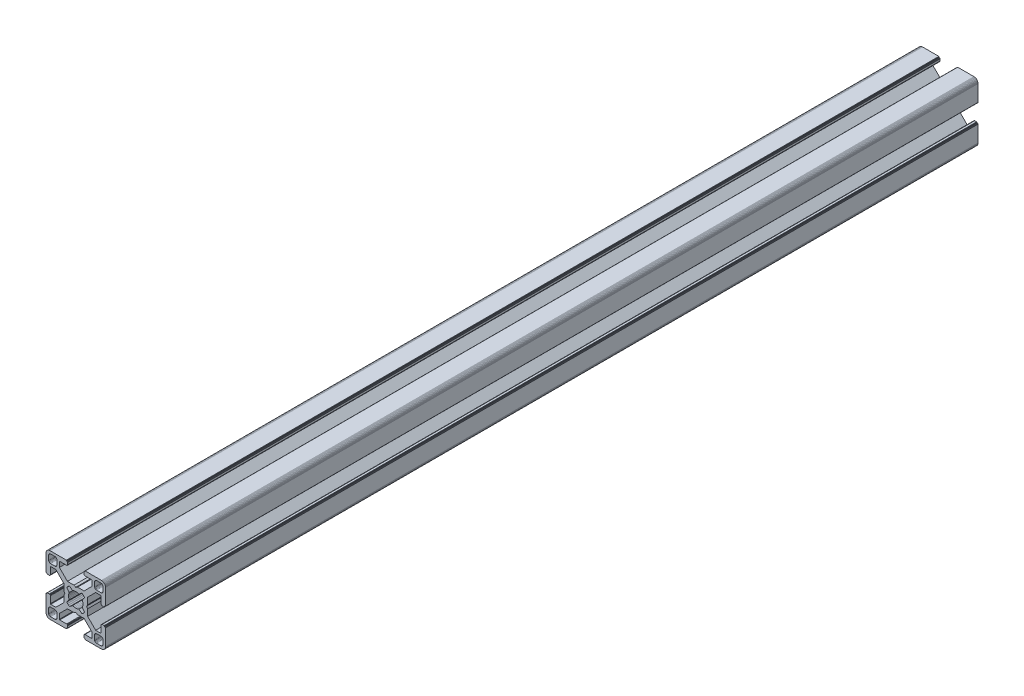
SolidWorks part; units mm, degrees
ref_plane "Front Plane" through (0, 0, 0) normal (0, 0, 1) x (1, 0, 0)
ref_plane "Top Plane" through (0, 0, 0) normal (0, 1, 0) x (1, 0, 0)
ref_plane "Right Plane" through (0, 0, 0) normal (1, 0, 0) x (0, 0, -1)
ref_plane "Plane1" through (0, 0, 0) normal (0, 0, 1) x (1, 0, 0)
sketch "Sketch1" plane through (0, 0, 0) normal (0, 0, 1) x (1, 0, 0)
  line L0 (28.3473, 29.9696) -> (28, 30)
  line L1 (28, 30) -> (19.75, 30)
  line L2 (19.75, 30) -> (19.7153, 29.997)
  line L3 (19.7153, 29.997) -> (19.6816, 29.9879)
  line L4 (19.6816, 29.9879) -> (19.65, 29.9732)
  line L5 (19.65, 29.9732) -> (19.6214, 29.9532)
  line L6 (19.6214, 29.9532) -> (19.5968, 29.9286)
  line L7 (19.5968, 29.9286) -> (19.5768, 29.9)
  line L8 (19.5768, 29.9) -> (19.5621, 29.8684)
  line L9 (19.5621, 29.8684) -> (19.553, 29.8347)
  line L10 (19.553, 29.8347) -> (19.55, 29.8)
  line L11 (19.55, 29.8) -> (19.55, 29.7)
  line L12 (19.55, 29.7) -> (19.547, 29.6653)
  line L13 (19.547, 29.6653) -> (19.5379, 29.6316)
  line L14 (19.5379, 29.6316) -> (19.5232, 29.6)
  line L15 (19.5232, 29.6) -> (19.5032, 29.5714)
  line L16 (19.5032, 29.5714) -> (19.4786, 29.5468)
  line L17 (19.4786, 29.5468) -> (19.45, 29.5268)
  line L18 (19.45, 29.5268) -> (19.4184, 29.5121)
  line L19 (19.4184, 29.5121) -> (19.3847, 29.503)
  line L20 (19.3847, 29.503) -> (19.35, 29.5)
  line L21 (19.35, 29.5) -> (19.25, 29.5)
  line L22 (19.25, 29.5) -> (19.2153, 29.497)
  line L23 (19.2153, 29.497) -> (19.1816, 29.4879)
  line L24 (19.1816, 29.4879) -> (19.15, 29.4732)
  line L25 (19.15, 29.4732) -> (19.1214, 29.4532)
  line L26 (19.1214, 29.4532) -> (19.0968, 29.4286)
  line L27 (19.0968, 29.4286) -> (19.0768, 29.4)
  line L28 (19.0768, 29.4) -> (19.0621, 29.3684)
  line L29 (19.0621, 29.3684) -> (19.053, 29.3347)
  line L30 (19.053, 29.3347) -> (19.05, 29.3)
  line L31 (19.05, 29.3) -> (19.05, 28.4)
  line L32 (19.05, 28.4) -> (19.0591, 28.2958)
  line L33 (19.0591, 28.2958) -> (19.0862, 28.1948)
  line L34 (19.0862, 28.1948) -> (19.1304, 28.1)
  line L35 (19.1304, 28.1) -> (19.1904, 28.0143)
  line L36 (19.1904, 28.0143) -> (19.2643, 27.9404)
  line L37 (19.2643, 27.9404) -> (19.35, 27.8804)
  line L38 (19.35, 27.8804) -> (19.4448, 27.8362)
  line L39 (19.4448, 27.8362) -> (19.5458, 27.8091)
  line L40 (19.5458, 27.8091) -> (19.65, 27.8)
  line L41 (19.65, 27.8) -> (23.05, 27.8)
  line L42 (23.05, 27.8) -> (23.0847, 27.7969)
  line L43 (23.0847, 27.7969) -> (23.1184, 27.7879)
  line L44 (23.1184, 27.7879) -> (23.15, 27.7732)
  line L45 (23.15, 27.7732) -> (23.1786, 27.7532)
  line L46 (23.1786, 27.7532) -> (23.2032, 27.7285)
  line L47 (23.2032, 27.7285) -> (23.2232, 27.7)
  line L48 (23.2232, 27.7) -> (23.2379, 27.6684)
  line L49 (23.2379, 27.6684) -> (23.247, 27.6347)
  line L50 (23.247, 27.6347) -> (23.25, 27.6)
  line L51 (23.25, 27.6) -> (23.25, 25.05)
  line L52 (23.25, 25.05) -> (19.2045, 21)
  line L53 (19.2045, 21) -> (15.9, 21)
  line L54 (15.9, 21) -> (15, 20.4848)
  line L55 (15, 20.4848) -> (14.1, 21)
  line L56 (14.1, 21) -> (10.7955, 21)
  line L57 (10.7955, 21) -> (7.9973, 23.8013)
  line L58 (7.9973, 23.8013) -> (6.75, 25.05)
  line L59 (6.75, 25.05) -> (6.75, 27.6)
  line L60 (6.75, 27.6) -> (6.753, 27.6347)
  line L61 (6.753, 27.6347) -> (6.7621, 27.6684)
  line L62 (6.7621, 27.6684) -> (6.7768, 27.7)
  line L63 (6.7768, 27.7) -> (6.7968, 27.7285)
  line L64 (6.7968, 27.7285) -> (6.8215, 27.7532)
  line L65 (6.8215, 27.7532) -> (6.85, 27.7732)
  line L66 (6.85, 27.7732) -> (6.8816, 27.7879)
  line L67 (6.8816, 27.7879) -> (6.9153, 27.7969)
  line L68 (6.9153, 27.7969) -> (6.95, 27.8)
  line L69 (6.95, 27.8) -> (10.35, 27.8)
  line L70 (10.35, 27.8) -> (10.4542, 27.8091)
  line L71 (10.4542, 27.8091) -> (10.5552, 27.8362)
  line L72 (10.5552, 27.8362) -> (10.65, 27.8804)
  line L73 (10.65, 27.8804) -> (10.7357, 27.9404)
  line L74 (10.7357, 27.9404) -> (10.8096, 28.0143)
  line L75 (10.8096, 28.0143) -> (10.8696, 28.1)
  line L76 (10.8696, 28.1) -> (10.9138, 28.1948)
  line L77 (10.9138, 28.1948) -> (10.9409, 28.2958)
  line L78 (10.9409, 28.2958) -> (10.95, 28.4)
  line L79 (10.95, 28.4) -> (10.95, 29.3)
  line L80 (10.95, 29.3) -> (10.947, 29.3347)
  line L81 (10.947, 29.3347) -> (10.938, 29.3684)
  line L82 (10.938, 29.3684) -> (10.9232, 29.4)
  line L83 (10.9232, 29.4) -> (10.9032, 29.4286)
  line L84 (10.9032, 29.4286) -> (10.8786, 29.4532)
  line L85 (10.8786, 29.4532) -> (10.85, 29.4732)
  line L86 (10.85, 29.4732) -> (10.8184, 29.4879)
  line L87 (10.8184, 29.4879) -> (10.7847, 29.497)
  line L88 (10.7847, 29.497) -> (10.75, 29.5)
  line L89 (10.75, 29.5) -> (10.65, 29.5)
  line L90 (10.65, 29.5) -> (10.6153, 29.503)
  line L91 (10.6153, 29.503) -> (10.5816, 29.5121)
  line L92 (10.5816, 29.5121) -> (10.55, 29.5268)
  line L93 (10.55, 29.5268) -> (10.5214, 29.5468)
  line L94 (10.5214, 29.5468) -> (10.4968, 29.5714)
  line L95 (10.4968, 29.5714) -> (10.4768, 29.6)
  line L96 (10.4768, 29.6) -> (10.4621, 29.6316)
  line L97 (10.4621, 29.6316) -> (10.453, 29.6653)
  line L98 (10.453, 29.6653) -> (10.45, 29.7)
  line L99 (10.45, 29.7) -> (10.45, 29.8)
  line L100 (10.45, 29.8) -> (10.447, 29.8347)
  line L101 (10.447, 29.8347) -> (10.4379, 29.8684)
  line L102 (10.4379, 29.8684) -> (10.4232, 29.9)
  line L103 (10.4232, 29.9) -> (10.4032, 29.9286)
  line L104 (10.4032, 29.9286) -> (10.3786, 29.9532)
  line L105 (10.3786, 29.9532) -> (10.35, 29.9732)
  line L106 (10.35, 29.9732) -> (10.3184, 29.9879)
  line L107 (10.3184, 29.9879) -> (10.2847, 29.997)
  line L108 (10.2847, 29.997) -> (10.25, 30)
  line L109 (10.25, 30) -> (2, 30)
  line L110 (2, 30) -> (1.6527, 29.9696)
  line L111 (1.6527, 29.9696) -> (1.316, 29.8794)
  line L112 (1.316, 29.8794) -> (1, 29.7321)
  line L113 (1, 29.7321) -> (0.7144, 29.5321)
  line L114 (0.7144, 29.5321) -> (0.4679, 29.2856)
  line L115 (0.4679, 29.2856) -> (0.2679, 29)
  line L116 (0.2679, 29) -> (0.1206, 28.684)
  line L117 (0.1206, 28.684) -> (0.0304, 28.3473)
  line L118 (0.0304, 28.3473) -> (0, 28)
  line L119 (0, 28) -> (0, 19.75)
  line L120 (0, 19.75) -> (0.003, 19.7153)
  line L121 (0.003, 19.7153) -> (0.0121, 19.6816)
  line L122 (0.0121, 19.6816) -> (0.0268, 19.65)
  line L123 (0.0268, 19.65) -> (0.0468, 19.6214)
  line L124 (0.0468, 19.6214) -> (0.0714, 19.5968)
  line L125 (0.0714, 19.5968) -> (0.1, 19.5768)
  line L126 (0.1, 19.5768) -> (0.1316, 19.5621)
  line L127 (0.1316, 19.5621) -> (0.1653, 19.553)
  line L128 (0.1653, 19.553) -> (0.2, 19.55)
  line L129 (0.2, 19.55) -> (0.3, 19.55)
  line L130 (0.3, 19.55) -> (0.3347, 19.547)
  line L131 (0.3347, 19.547) -> (0.3684, 19.5379)
  line L132 (0.3684, 19.5379) -> (0.4, 19.5232)
  line L133 (0.4, 19.5232) -> (0.4286, 19.5032)
  line L134 (0.4286, 19.5032) -> (0.4532, 19.4786)
  line L135 (0.4532, 19.4786) -> (0.4732, 19.45)
  line L136 (0.4732, 19.45) -> (0.4879, 19.4184)
  line L137 (0.4879, 19.4184) -> (0.497, 19.3847)
  line L138 (0.497, 19.3847) -> (0.5, 19.35)
  line L139 (0.5, 19.35) -> (0.5, 19.25)
  line L140 (0.5, 19.25) -> (0.503, 19.2153)
  line L141 (0.503, 19.2153) -> (0.5121, 19.1816)
  line L142 (0.5121, 19.1816) -> (0.5268, 19.15)
  line L143 (0.5268, 19.15) -> (0.5468, 19.1214)
  line L144 (0.5468, 19.1214) -> (0.5714, 19.0968)
  line L145 (0.5714, 19.0968) -> (0.6, 19.0768)
  line L146 (0.6, 19.0768) -> (0.6316, 19.0621)
  line L147 (0.6316, 19.0621) -> (0.6653, 19.053)
  line L148 (0.6653, 19.053) -> (0.7, 19.05)
  line L149 (0.7, 19.05) -> (1.6, 19.05)
  line L150 (1.6, 19.05) -> (1.7042, 19.0591)
  line L151 (1.7042, 19.0591) -> (1.8052, 19.0862)
  line L152 (1.8052, 19.0862) -> (1.9, 19.1304)
  line L153 (1.9, 19.1304) -> (1.9857, 19.1904)
  line L154 (1.9857, 19.1904) -> (2.0596, 19.2643)
  line L155 (2.0596, 19.2643) -> (2.1196, 19.35)
  line L156 (2.1196, 19.35) -> (2.1638, 19.4448)
  line L157 (2.1638, 19.4448) -> (2.1909, 19.5458)
  line L158 (2.1909, 19.5458) -> (2.2, 19.65)
  line L159 (2.2, 19.65) -> (2.2, 23.05)
  line L160 (2.2, 23.05) -> (2.203, 23.0847)
  line L161 (2.203, 23.0847) -> (2.2121, 23.1184)
  line L162 (2.2121, 23.1184) -> (2.2268, 23.15)
  line L163 (2.2268, 23.15) -> (2.2468, 23.1786)
  line L164 (2.2468, 23.1786) -> (2.2714, 23.2032)
  line L165 (2.2714, 23.2032) -> (2.3, 23.2232)
  line L166 (2.3, 23.2232) -> (2.3316, 23.2379)
  line L167 (2.3316, 23.2379) -> (2.3653, 23.247)
  line L168 (2.3653, 23.247) -> (2.4, 23.25)
  line L169 (2.4, 23.25) -> (4.95, 23.25)
  line L170 (4.95, 23.25) -> (7.9973, 20.2027)
  line L171 (7.9973, 20.2027) -> (8.9955, 19.2045)
  line L172 (8.9955, 19.2045) -> (8.9955, 15.9)
  line L173 (8.9955, 15.9) -> (9.5151, 15)
  line L174 (9.5151, 15) -> (8.9955, 14.1)
  line L175 (8.9955, 14.1) -> (8.9955, 10.7955)
  line L176 (8.9955, 10.7955) -> (4.95, 6.75)
  line L177 (4.95, 6.75) -> (2.4, 6.75)
  line L178 (2.4, 6.75) -> (2.3653, 6.753)
  line L179 (2.3653, 6.753) -> (2.3316, 6.7621)
  line L180 (2.3316, 6.7621) -> (2.3, 6.7768)
  line L181 (2.3, 6.7768) -> (2.2714, 6.7968)
  line L182 (2.2714, 6.7968) -> (2.2468, 6.8214)
  line L183 (2.2468, 6.8214) -> (2.2268, 6.85)
  line L184 (2.2268, 6.85) -> (2.2121, 6.8816)
  line L185 (2.2121, 6.8816) -> (2.203, 6.9153)
  line L186 (2.203, 6.9153) -> (2.2, 6.95)
  line L187 (2.2, 6.95) -> (2.2, 10.35)
  line L188 (2.2, 10.35) -> (2.1909, 10.4542)
  line L189 (2.1909, 10.4542) -> (2.1638, 10.5552)
  line L190 (2.1638, 10.5552) -> (2.1196, 10.65)
  line L191 (2.1196, 10.65) -> (2.0596, 10.7357)
  line L192 (2.0596, 10.7357) -> (1.9857, 10.8096)
  line L193 (1.9857, 10.8096) -> (1.9, 10.8696)
  line L194 (1.9, 10.8696) -> (1.8052, 10.9138)
  line L195 (1.8052, 10.9138) -> (1.7042, 10.9409)
  line L196 (1.7042, 10.9409) -> (1.6, 10.95)
  line L197 (1.6, 10.95) -> (0.7, 10.95)
  line L198 (0.7, 10.95) -> (0.6653, 10.9469)
  line L199 (0.6653, 10.9469) -> (0.6316, 10.9379)
  line L200 (0.6316, 10.9379) -> (0.6, 10.9232)
  line L201 (0.6, 10.9232) -> (0.5715, 10.9032)
  line L202 (0.5715, 10.9032) -> (0.5468, 10.8785)
  line L203 (0.5468, 10.8785) -> (0.5268, 10.85)
  line L204 (0.5268, 10.85) -> (0.5121, 10.8184)
  line L205 (0.5121, 10.8184) -> (0.503, 10.7847)
  line L206 (0.503, 10.7847) -> (0.5, 10.75)
  line L207 (0.5, 10.75) -> (0.5, 10.65)
  line L208 (0.5, 10.65) -> (0.497, 10.6153)
  line L209 (0.497, 10.6153) -> (0.4879, 10.5816)
  line L210 (0.4879, 10.5816) -> (0.4732, 10.55)
  line L211 (0.4732, 10.55) -> (0.4532, 10.5214)
  line L212 (0.4532, 10.5214) -> (0.4286, 10.4968)
  line L213 (0.4286, 10.4968) -> (0.4, 10.4768)
  line L214 (0.4, 10.4768) -> (0.3684, 10.4621)
  line L215 (0.3684, 10.4621) -> (0.3347, 10.453)
  line L216 (0.3347, 10.453) -> (0.3, 10.45)
  line L217 (0.3, 10.45) -> (0.2, 10.45)
  line L218 (0.2, 10.45) -> (0.1653, 10.447)
  line L219 (0.1653, 10.447) -> (0.1316, 10.4379)
  line L220 (0.1316, 10.4379) -> (0.1, 10.4232)
  line L221 (0.1, 10.4232) -> (0.0714, 10.4032)
  line L222 (0.0714, 10.4032) -> (0.0468, 10.3786)
  line L223 (0.0468, 10.3786) -> (0.0268, 10.35)
  line L224 (0.0268, 10.35) -> (0.0121, 10.3184)
  line L225 (0.0121, 10.3184) -> (0.003, 10.2847)
  line L226 (0.003, 10.2847) -> (0, 10.25)
  line L227 (0, 10.25) -> (0, 2)
  line L228 (0, 2) -> (0.0304, 1.6527)
  line L229 (0.0304, 1.6527) -> (0.1206, 1.316)
  line L230 (0.1206, 1.316) -> (0.2679, 1)
  line L231 (0.2679, 1) -> (0.4679, 0.7144)
  line L232 (0.4679, 0.7144) -> (0.7144, 0.4679)
  line L233 (0.7144, 0.4679) -> (1, 0.2679)
  line L234 (1, 0.2679) -> (1.316, 0.1206)
  line L235 (1.316, 0.1206) -> (1.6527, 0.0304)
  line L236 (1.6527, 0.0304) -> (2, 0)
  line L237 (2, 0) -> (10.25, 0)
  line L238 (10.25, 0) -> (10.2847, 0.003)
  line L239 (10.2847, 0.003) -> (10.3184, 0.0121)
  line L240 (10.3184, 0.0121) -> (10.35, 0.0268)
  line L241 (10.35, 0.0268) -> (10.3786, 0.0468)
  line L242 (10.3786, 0.0468) -> (10.4032, 0.0714)
  line L243 (10.4032, 0.0714) -> (10.4232, 0.1)
  line L244 (10.4232, 0.1) -> (10.4379, 0.1316)
  line L245 (10.4379, 0.1316) -> (10.447, 0.1653)
  line L246 (10.447, 0.1653) -> (10.45, 0.2)
  line L247 (10.45, 0.2) -> (10.45, 0.3)
  line L248 (10.45, 0.3) -> (10.453, 0.3347)
  line L249 (10.453, 0.3347) -> (10.4621, 0.3684)
  line L250 (10.4621, 0.3684) -> (10.4768, 0.4)
  line L251 (10.4768, 0.4) -> (10.4968, 0.4286)
  line L252 (10.4968, 0.4286) -> (10.5214, 0.4532)
  line L253 (10.5214, 0.4532) -> (10.55, 0.4732)
  line L254 (10.55, 0.4732) -> (10.5816, 0.4879)
  line L255 (10.5816, 0.4879) -> (10.6153, 0.497)
  line L256 (10.6153, 0.497) -> (10.65, 0.5)
  line L257 (10.65, 0.5) -> (10.75, 0.5)
  line L258 (10.75, 0.5) -> (10.7847, 0.503)
  line L259 (10.7847, 0.503) -> (10.8184, 0.5121)
  line L260 (10.8184, 0.5121) -> (10.85, 0.5268)
  line L261 (10.85, 0.5268) -> (10.8785, 0.5468)
  line L262 (10.8785, 0.5468) -> (10.9032, 0.5715)
  line L263 (10.9032, 0.5715) -> (10.9232, 0.6)
  line L264 (10.9232, 0.6) -> (10.9379, 0.6316)
  line L265 (10.9379, 0.6316) -> (10.9469, 0.6653)
  line L266 (10.9469, 0.6653) -> (10.95, 0.7)
  line L267 (10.95, 0.7) -> (10.95, 1.6)
  line L268 (10.95, 1.6) -> (10.9409, 1.7042)
  line L269 (10.9409, 1.7042) -> (10.9138, 1.8052)
  line L270 (10.9138, 1.8052) -> (10.8696, 1.9)
  line L271 (10.8696, 1.9) -> (10.8096, 1.9857)
  line L272 (10.8096, 1.9857) -> (10.7357, 2.0596)
  line L273 (10.7357, 2.0596) -> (10.65, 2.1196)
  line L274 (10.65, 2.1196) -> (10.5552, 2.1638)
  line L275 (10.5552, 2.1638) -> (10.4542, 2.1909)
  line L276 (10.4542, 2.1909) -> (10.35, 2.2)
  line L277 (10.35, 2.2) -> (6.95, 2.2)
  line L278 (6.95, 2.2) -> (6.9153, 2.203)
  line L279 (6.9153, 2.203) -> (6.8816, 2.212)
  line L280 (6.8816, 2.212) -> (6.85, 2.2268)
  line L281 (6.85, 2.2268) -> (6.8215, 2.2468)
  line L282 (6.8215, 2.2468) -> (6.7968, 2.2714)
  line L283 (6.7968, 2.2714) -> (6.7768, 2.3)
  line L284 (6.7768, 2.3) -> (6.7621, 2.3316)
  line L285 (6.7621, 2.3316) -> (6.753, 2.3653)
  line L286 (6.753, 2.3653) -> (6.75, 2.4)
  line L287 (6.75, 2.4) -> (6.75, 4.95)
  line L288 (6.75, 4.95) -> (9.7875, 7.9908)
  line L289 (9.7875, 7.9908) -> (10.7955, 9)
  line L290 (10.7955, 9) -> (14.1, 9)
  line L291 (14.1, 9) -> (15, 9.5151)
  line L292 (15, 9.5151) -> (15.9, 9)
  line L293 (15.9, 9) -> (19.2045, 9)
  line L294 (19.2045, 9) -> (20.2126, 7.9908)
  line L295 (20.2126, 7.9908) -> (23.25, 4.95)
  line L296 (23.25, 4.95) -> (23.25, 2.4)
  line L297 (23.25, 2.4) -> (23.247, 2.3653)
  line L298 (23.247, 2.3653) -> (23.2379, 2.3316)
  line L299 (23.2379, 2.3316) -> (23.2232, 2.3)
  line L300 (23.2232, 2.3) -> (23.2032, 2.2714)
  line L301 (23.2032, 2.2714) -> (23.1786, 2.2468)
  line L302 (23.1786, 2.2468) -> (23.15, 2.2268)
  line L303 (23.15, 2.2268) -> (23.1184, 2.212)
  line L304 (23.1184, 2.212) -> (23.0847, 2.203)
  line L305 (23.0847, 2.203) -> (23.05, 2.2)
  line L306 (23.05, 2.2) -> (19.65, 2.2)
  line L307 (19.65, 2.2) -> (19.5458, 2.1909)
  line L308 (19.5458, 2.1909) -> (19.4448, 2.1638)
  line L309 (19.4448, 2.1638) -> (19.35, 2.1196)
  line L310 (19.35, 2.1196) -> (19.2643, 2.0596)
  line L311 (19.2643, 2.0596) -> (19.1904, 1.9857)
  line L312 (19.1904, 1.9857) -> (19.1304, 1.9)
  line L313 (19.1304, 1.9) -> (19.0862, 1.8052)
  line L314 (19.0862, 1.8052) -> (19.0591, 1.7042)
  line L315 (19.0591, 1.7042) -> (19.05, 1.6)
  line L316 (19.05, 1.6) -> (19.05, 0.7)
  line L317 (19.05, 0.7) -> (19.053, 0.6653)
  line L318 (19.053, 0.6653) -> (19.0621, 0.6316)
  line L319 (19.0621, 0.6316) -> (19.0768, 0.6)
  line L320 (19.0768, 0.6) -> (19.0968, 0.5714)
  line L321 (19.0968, 0.5714) -> (19.1214, 0.5468)
  line L322 (19.1214, 0.5468) -> (19.15, 0.5268)
  line L323 (19.15, 0.5268) -> (19.1816, 0.5121)
  line L324 (19.1816, 0.5121) -> (19.2153, 0.503)
  line L325 (19.2153, 0.503) -> (19.25, 0.5)
  line L326 (19.25, 0.5) -> (19.35, 0.5)
  line L327 (19.35, 0.5) -> (19.3847, 0.497)
  line L328 (19.3847, 0.497) -> (19.4184, 0.4879)
  line L329 (19.4184, 0.4879) -> (19.45, 0.4732)
  line L330 (19.45, 0.4732) -> (19.4786, 0.4532)
  line L331 (19.4786, 0.4532) -> (19.5032, 0.4286)
  line L332 (19.5032, 0.4286) -> (19.5232, 0.4)
  line L333 (19.5232, 0.4) -> (19.5379, 0.3684)
  line L334 (19.5379, 0.3684) -> (19.547, 0.3347)
  line L335 (19.547, 0.3347) -> (19.55, 0.3)
  line L336 (19.55, 0.3) -> (19.55, 0.2)
  line L337 (19.55, 0.2) -> (19.553, 0.1653)
  line L338 (19.553, 0.1653) -> (19.5621, 0.1316)
  line L339 (19.5621, 0.1316) -> (19.5768, 0.1)
  line L340 (19.5768, 0.1) -> (19.5968, 0.0714)
  line L341 (19.5968, 0.0714) -> (19.6214, 0.0468)
  line L342 (19.6214, 0.0468) -> (19.65, 0.0268)
  line L343 (19.65, 0.0268) -> (19.6816, 0.0121)
  line L344 (19.6816, 0.0121) -> (19.7153, 0.003)
  line L345 (19.7153, 0.003) -> (19.75, 0)
  line L346 (19.75, 0) -> (28, 0)
  line L347 (28, 0) -> (28.3473, 0.0304)
  line L348 (28.3473, 0.0304) -> (28.684, 0.1206)
  line L349 (28.684, 0.1206) -> (29, 0.2679)
  line L350 (29, 0.2679) -> (29.2856, 0.4679)
  line L351 (29.2856, 0.4679) -> (29.5321, 0.7144)
  line L352 (29.5321, 0.7144) -> (29.7321, 1)
  line L353 (29.7321, 1) -> (29.8794, 1.316)
  line L354 (29.8794, 1.316) -> (29.9696, 1.6527)
  line L355 (29.9696, 1.6527) -> (30, 2)
  line L356 (30, 2) -> (30, 10.25)
  line L357 (30, 10.25) -> (29.997, 10.2847)
  line L358 (29.997, 10.2847) -> (29.988, 10.3184)
  line L359 (29.988, 10.3184) -> (29.9732, 10.35)
  line L360 (29.9732, 10.35) -> (29.9532, 10.3785)
  line L361 (29.9532, 10.3785) -> (29.9286, 10.4032)
  line L362 (29.9286, 10.4032) -> (29.9, 10.4232)
  line L363 (29.9, 10.4232) -> (29.8684, 10.4379)
  line L364 (29.8684, 10.4379) -> (29.8347, 10.447)
  line L365 (29.8347, 10.447) -> (29.8, 10.45)
  line L366 (29.8, 10.45) -> (29.7, 10.45)
  line L367 (29.7, 10.45) -> (29.6649, 10.4534)
  line L368 (29.6649, 10.4534) -> (29.6312, 10.4624)
  line L369 (29.6312, 10.4624) -> (29.5996, 10.4772)
  line L370 (29.5996, 10.4772) -> (29.5711, 10.4972)
  line L371 (29.5711, 10.4972) -> (29.5464, 10.5218)
  line L372 (29.5464, 10.5218) -> (29.5264, 10.5504)
  line L373 (29.5264, 10.5504) -> (29.5117, 10.582)
  line L374 (29.5117, 10.582) -> (29.5027, 10.6156)
  line L375 (29.5027, 10.6156) -> (29.4996, 10.6504)
  line L376 (29.4996, 10.6504) -> (29.4996, 10.7504)
  line L377 (29.4996, 10.7504) -> (29.497, 10.7847)
  line L378 (29.497, 10.7847) -> (29.4879, 10.8184)
  line L379 (29.4879, 10.8184) -> (29.4732, 10.85)
  line L380 (29.4732, 10.85) -> (29.4532, 10.8785)
  line L381 (29.4532, 10.8785) -> (29.4286, 10.9032)
  line L382 (29.4286, 10.9032) -> (29.4, 10.9232)
  line L383 (29.4, 10.9232) -> (29.3684, 10.9379)
  line L384 (29.3684, 10.9379) -> (29.3347, 10.9469)
  line L385 (29.3347, 10.9469) -> (29.3, 10.95)
  line L386 (29.3, 10.95) -> (28.4, 10.95)
  line L387 (28.4, 10.95) -> (28.2958, 10.9409)
  line L388 (28.2958, 10.9409) -> (28.1948, 10.9138)
  line L389 (28.1948, 10.9138) -> (28.1, 10.8696)
  line L390 (28.1, 10.8696) -> (28.0143, 10.8096)
  line L391 (28.0143, 10.8096) -> (27.9404, 10.7357)
  line L392 (27.9404, 10.7357) -> (27.8804, 10.65)
  line L393 (27.8804, 10.65) -> (27.8362, 10.5552)
  line L394 (27.8362, 10.5552) -> (27.8091, 10.4542)
  line L395 (27.8091, 10.4542) -> (27.8, 10.35)
  line L396 (27.8, 10.35) -> (27.8, 6.95)
  line L397 (27.8, 6.95) -> (27.797, 6.9153)
  line L398 (27.797, 6.9153) -> (27.7879, 6.8816)
  line L399 (27.7879, 6.8816) -> (27.7732, 6.85)
  line L400 (27.7732, 6.85) -> (27.7532, 6.8214)
  line L401 (27.7532, 6.8214) -> (27.7286, 6.7968)
  line L402 (27.7286, 6.7968) -> (27.7, 6.7768)
  line L403 (27.7, 6.7768) -> (27.6684, 6.7621)
  line L404 (27.6684, 6.7621) -> (27.6347, 6.753)
  line L405 (27.6347, 6.753) -> (27.6, 6.75)
  line L406 (27.6, 6.75) -> (25.05, 6.75)
  line L407 (25.05, 6.75) -> (23.8092, 7.9908)
  line L408 (23.8092, 7.9908) -> (21.0045, 10.7955)
  line L409 (21.0045, 10.7955) -> (21.0045, 14.1)
  line L410 (21.0045, 14.1) -> (20.4849, 15)
  line L411 (20.4849, 15) -> (21.0045, 15.9)
  line L412 (21.0045, 15.9) -> (21.0045, 19.2045)
  line L413 (21.0045, 19.2045) -> (25.05, 23.25)
  line L414 (25.05, 23.25) -> (27.6, 23.25)
  line L415 (27.6, 23.25) -> (27.6347, 23.247)
  line L416 (27.6347, 23.247) -> (27.6684, 23.2379)
  line L417 (27.6684, 23.2379) -> (27.7, 23.2232)
  line L418 (27.7, 23.2232) -> (27.7286, 23.2032)
  line L419 (27.7286, 23.2032) -> (27.7532, 23.1786)
  line L420 (27.7532, 23.1786) -> (27.7732, 23.15)
  line L421 (27.7732, 23.15) -> (27.7879, 23.1184)
  line L422 (27.7879, 23.1184) -> (27.797, 23.0847)
  line L423 (27.797, 23.0847) -> (27.8, 23.05)
  line L424 (27.8, 23.05) -> (27.8, 19.65)
  line L425 (27.8, 19.65) -> (27.8091, 19.5458)
  line L426 (27.8091, 19.5458) -> (27.8362, 19.4448)
  line L427 (27.8362, 19.4448) -> (27.8804, 19.35)
  line L428 (27.8804, 19.35) -> (27.9404, 19.2643)
  line L429 (27.9404, 19.2643) -> (28.0143, 19.1904)
  line L430 (28.0143, 19.1904) -> (28.1, 19.1304)
  line L431 (28.1, 19.1304) -> (28.1948, 19.0862)
  line L432 (28.1948, 19.0862) -> (28.2958, 19.0591)
  line L433 (28.2958, 19.0591) -> (28.4, 19.05)
  line L434 (28.4, 19.05) -> (29.3, 19.05)
  line L435 (29.3, 19.05) -> (29.3347, 19.053)
  line L436 (29.3347, 19.053) -> (29.3684, 19.0621)
  line L437 (29.3684, 19.0621) -> (29.4, 19.0768)
  line L438 (29.4, 19.0768) -> (29.4282, 19.0971)
  line L439 (29.4282, 19.0971) -> (29.4528, 19.1218)
  line L440 (29.4528, 19.1218) -> (29.4728, 19.1504)
  line L441 (29.4728, 19.1504) -> (29.4876, 19.182)
  line L442 (29.4876, 19.182) -> (29.4966, 19.2156)
  line L443 (29.4966, 19.2156) -> (29.4996, 19.2504)
  line L444 (29.4996, 19.2504) -> (29.4996, 19.3504)
  line L445 (29.4996, 19.3504) -> (29.5027, 19.3851)
  line L446 (29.5027, 19.3851) -> (29.5117, 19.4188)
  line L447 (29.5117, 19.4188) -> (29.5264, 19.4504)
  line L448 (29.5264, 19.4504) -> (29.5464, 19.4789)
  line L449 (29.5464, 19.4789) -> (29.5711, 19.5036)
  line L450 (29.5711, 19.5036) -> (29.5996, 19.5236)
  line L451 (29.5996, 19.5236) -> (29.6312, 19.5383)
  line L452 (29.6312, 19.5383) -> (29.6649, 19.5473)
  line L453 (29.6649, 19.5473) -> (29.7, 19.55)
  line L454 (29.7, 19.55) -> (29.8, 19.55)
  line L455 (29.8, 19.55) -> (29.8347, 19.553)
  line L456 (29.8347, 19.553) -> (29.8684, 19.5621)
  line L457 (29.8684, 19.5621) -> (29.9, 19.5768)
  line L458 (29.9, 19.5768) -> (29.9286, 19.5968)
  line L459 (29.9286, 19.5968) -> (29.9532, 19.6214)
  line L460 (29.9532, 19.6214) -> (29.9732, 19.65)
  line L461 (29.9732, 19.65) -> (29.9879, 19.6816)
  line L462 (29.9879, 19.6816) -> (29.997, 19.7153)
  line L463 (29.997, 19.7153) -> (30, 19.75)
  line L464 (30, 19.75) -> (30, 28)
  line L465 (30, 28) -> (29.9696, 28.3473)
  line L466 (29.9696, 28.3473) -> (29.8794, 28.684)
  line L467 (29.8794, 28.684) -> (29.7321, 29)
  line L468 (29.7321, 29) -> (29.5321, 29.2856)
  line L469 (29.5321, 29.2856) -> (29.2856, 29.5321)
  line L470 (29.2856, 29.5321) -> (29, 29.7321)
  line L471 (29, 29.7321) -> (28.684, 29.8794)
  line L472 (28.684, 29.8794) -> (28.3473, 29.9696)
  line L473 (1.3, 25.5) -> (1.3, 27.7)
  line L474 (1.3, 27.7) -> (1.3123, 27.8564)
  line L475 (1.3123, 27.8564) -> (1.3489, 28.009)
  line L476 (1.3489, 28.009) -> (1.409, 28.154)
  line L477 (1.409, 28.154) -> (1.491, 28.2878)
  line L478 (1.491, 28.2878) -> (1.5929, 28.4071)
  line L479 (1.5929, 28.4071) -> (1.7122, 28.509)
  line L480 (1.7122, 28.509) -> (1.846, 28.591)
  line L481 (1.846, 28.591) -> (1.991, 28.6511)
  line L482 (1.991, 28.6511) -> (2.1436, 28.6877)
  line L483 (2.1436, 28.6877) -> (2.3, 28.7)
  line L484 (2.3, 28.7) -> (4.5, 28.7)
  line L485 (4.5, 28.7) -> (4.6564, 28.6877)
  line L486 (4.6564, 28.6877) -> (4.809, 28.6511)
  line L487 (4.809, 28.6511) -> (4.954, 28.591)
  line L488 (4.954, 28.591) -> (5.0878, 28.509)
  line L489 (5.0878, 28.509) -> (5.2071, 28.4071)
  line L490 (5.2071, 28.4071) -> (5.309, 28.2878)
  line L491 (5.309, 28.2878) -> (5.391, 28.154)
  line L492 (5.391, 28.154) -> (5.4511, 28.009)
  line L493 (5.4511, 28.009) -> (5.4877, 27.8564)
  line L494 (5.4877, 27.8564) -> (5.5, 27.7)
  line L495 (5.5, 27.7) -> (5.5, 25.5)
  line L496 (5.5, 25.5) -> (5.4877, 25.3436)
  line L497 (5.4877, 25.3436) -> (5.4511, 25.191)
  line L498 (5.4511, 25.191) -> (5.391, 25.046)
  line L499 (5.391, 25.046) -> (5.309, 24.9122)
  line L500 (5.309, 24.9122) -> (5.2071, 24.7929)
  line L501 (5.2071, 24.7929) -> (5.0878, 24.691)
  line L502 (5.0878, 24.691) -> (4.954, 24.609)
  line L503 (4.954, 24.609) -> (4.809, 24.5489)
  line L504 (4.809, 24.5489) -> (4.6564, 24.5123)
  line L505 (4.6564, 24.5123) -> (4.5, 24.5)
  line L506 (4.5, 24.5) -> (2.3, 24.5)
  line L507 (2.3, 24.5) -> (2.1436, 24.5123)
  line L508 (2.1436, 24.5123) -> (1.991, 24.5489)
  line L509 (1.991, 24.5489) -> (1.846, 24.609)
  line L510 (1.846, 24.609) -> (1.7122, 24.691)
  line L511 (1.7122, 24.691) -> (1.5929, 24.7929)
  line L512 (1.5929, 24.7929) -> (1.491, 24.9122)
  line L513 (1.491, 24.9122) -> (1.409, 25.046)
  line L514 (1.409, 25.046) -> (1.3489, 25.191)
  line L515 (1.3489, 25.191) -> (1.3123, 25.3436)
  line L516 (1.3123, 25.3436) -> (1.3, 25.5)
  line L517 (25.3436, 28.6877) -> (25.5, 28.7)
  line L518 (25.5, 28.7) -> (27.7, 28.7)
  line L519 (27.7, 28.7) -> (27.8564, 28.6877)
  line L520 (27.8564, 28.6877) -> (28.009, 28.6511)
  line L521 (28.009, 28.6511) -> (28.154, 28.591)
  line L522 (28.154, 28.591) -> (28.2878, 28.509)
  line L523 (28.2878, 28.509) -> (28.4071, 28.4071)
  line L524 (28.4071, 28.4071) -> (28.509, 28.2878)
  line L525 (28.509, 28.2878) -> (28.591, 28.154)
  line L526 (28.591, 28.154) -> (28.6511, 28.009)
  line L527 (28.6511, 28.009) -> (28.6877, 27.8564)
  line L528 (28.6877, 27.8564) -> (28.7, 27.7)
  line L529 (28.7, 27.7) -> (28.7, 25.5)
  line L530 (28.7, 25.5) -> (28.6877, 25.3436)
  line L531 (28.6877, 25.3436) -> (28.6511, 25.191)
  line L532 (28.6511, 25.191) -> (28.591, 25.046)
  line L533 (28.591, 25.046) -> (28.509, 24.9122)
  line L534 (28.509, 24.9122) -> (28.4071, 24.7929)
  line L535 (28.4071, 24.7929) -> (28.2878, 24.691)
  line L536 (28.2878, 24.691) -> (28.154, 24.609)
  line L537 (28.154, 24.609) -> (28.009, 24.5489)
  line L538 (28.009, 24.5489) -> (27.8564, 24.5123)
  line L539 (27.8564, 24.5123) -> (27.7, 24.5)
  line L540 (27.7, 24.5) -> (25.5, 24.5)
  line L541 (25.5, 24.5) -> (25.3436, 24.5123)
  line L542 (25.3436, 24.5123) -> (25.191, 24.5489)
  line L543 (25.191, 24.5489) -> (25.046, 24.609)
  line L544 (25.046, 24.609) -> (24.9122, 24.691)
  line L545 (24.9122, 24.691) -> (24.7929, 24.7929)
  line L546 (24.7929, 24.7929) -> (24.691, 24.9122)
  line L547 (24.691, 24.9122) -> (24.609, 25.046)
  line L548 (24.609, 25.046) -> (24.5489, 25.191)
  line L549 (24.5489, 25.191) -> (24.5123, 25.3436)
  line L550 (24.5123, 25.3436) -> (24.5, 25.5)
  line L551 (24.5, 25.5) -> (24.5, 27.7)
  line L552 (24.5, 27.7) -> (24.5123, 27.8564)
  line L553 (24.5123, 27.8564) -> (24.5489, 28.009)
  line L554 (24.5489, 28.009) -> (24.609, 28.154)
  line L555 (24.609, 28.154) -> (24.691, 28.2878)
  line L556 (24.691, 28.2878) -> (24.7929, 28.4071)
  line L557 (24.7929, 28.4071) -> (24.9122, 28.509)
  line L558 (24.9122, 28.509) -> (25.046, 28.591)
  line L559 (25.046, 28.591) -> (25.191, 28.6511)
  line L560 (25.191, 28.6511) -> (25.3436, 28.6877)
  line L561 (15, 18.65) -> (15.55, 18.6083)
  line L562 (15.55, 18.6083) -> (16.0875, 18.4842)
  line L563 (16.0875, 18.4842) -> (16.6001, 18.2806)
  line L564 (16.6001, 18.2806) -> (18.1359, 19.5184)
  line L565 (18.1359, 19.5184) -> (18.645, 19.1187)
  line L566 (18.645, 19.1187) -> (19.1036, 18.6621)
  line L567 (19.1036, 18.6621) -> (19.5053, 18.1547)
  line L568 (19.5053, 18.1547) -> (18.2806, 16.6001)
  line L569 (18.2806, 16.6001) -> (18.4842, 16.0875)
  line L570 (18.4842, 16.0875) -> (18.6083, 15.55)
  line L571 (18.6083, 15.55) -> (18.65, 15)
  line L572 (18.65, 15) -> (18.6083, 14.45)
  line L573 (18.6083, 14.45) -> (18.4842, 13.9125)
  line L574 (18.4842, 13.9125) -> (18.2806, 13.3999)
  line L575 (18.2806, 13.3999) -> (19.5053, 11.8453)
  line L576 (19.5053, 11.8453) -> (19.1036, 11.3379)
  line L577 (19.1036, 11.3379) -> (18.645, 10.8813)
  line L578 (18.645, 10.8813) -> (18.1359, 10.4816)
  line L579 (18.1359, 10.4816) -> (16.6001, 11.7194)
  line L580 (16.6001, 11.7194) -> (16.0875, 11.5158)
  line L581 (16.0875, 11.5158) -> (15.55, 11.3917)
  line L582 (15.55, 11.3917) -> (15, 11.35)
  line L583 (15, 11.35) -> (14.45, 11.3917)
  line L584 (14.45, 11.3917) -> (13.9125, 11.5158)
  line L585 (13.9125, 11.5158) -> (13.3999, 11.7194)
  line L586 (13.3999, 11.7194) -> (11.8641, 10.4816)
  line L587 (11.8641, 10.4816) -> (11.355, 10.8813)
  line L588 (11.355, 10.8813) -> (10.8964, 11.3379)
  line L589 (10.8964, 11.3379) -> (10.4947, 11.8453)
  line L590 (10.4947, 11.8453) -> (11.7194, 13.3999)
  line L591 (11.7194, 13.3999) -> (11.5158, 13.9125)
  line L592 (11.5158, 13.9125) -> (11.3917, 14.45)
  line L593 (11.3917, 14.45) -> (11.35, 15)
  line L594 (11.35, 15) -> (11.3917, 15.55)
  line L595 (11.3917, 15.55) -> (11.5158, 16.0875)
  line L596 (11.5158, 16.0875) -> (11.7194, 16.6001)
  line L597 (11.7194, 16.6001) -> (10.4947, 18.1547)
  line L598 (10.4947, 18.1547) -> (10.8964, 18.6621)
  line L599 (10.8964, 18.6621) -> (11.355, 19.1187)
  line L600 (11.355, 19.1187) -> (11.8641, 19.5184)
  line L601 (11.8641, 19.5184) -> (13.3999, 18.2806)
  line L602 (13.3999, 18.2806) -> (13.9125, 18.4842)
  line L603 (13.9125, 18.4842) -> (14.45, 18.6083)
  line L604 (14.45, 18.6083) -> (15, 18.65)
  line L605 (4.5, 1.3) -> (2.3, 1.3)
  line L606 (2.3, 1.3) -> (2.1436, 1.3123)
  line L607 (2.1436, 1.3123) -> (1.991, 1.3489)
  line L608 (1.991, 1.3489) -> (1.846, 1.409)
  line L609 (1.846, 1.409) -> (1.7122, 1.491)
  line L610 (1.7122, 1.491) -> (1.5929, 1.5929)
  line L611 (1.5929, 1.5929) -> (1.491, 1.7122)
  line L612 (1.491, 1.7122) -> (1.409, 1.846)
  line L613 (1.409, 1.846) -> (1.3489, 1.991)
  line L614 (1.3489, 1.991) -> (1.3123, 2.1436)
  line L615 (1.3123, 2.1436) -> (1.3, 2.3)
  line L616 (1.3, 2.3) -> (1.3, 4.5)
  line L617 (1.3, 4.5) -> (1.3123, 4.6564)
  line L618 (1.3123, 4.6564) -> (1.3489, 4.809)
  line L619 (1.3489, 4.809) -> (1.409, 4.954)
  line L620 (1.409, 4.954) -> (1.491, 5.0878)
  line L621 (1.491, 5.0878) -> (1.5929, 5.2071)
  line L622 (1.5929, 5.2071) -> (1.7122, 5.309)
  line L623 (1.7122, 5.309) -> (1.846, 5.391)
  line L624 (1.846, 5.391) -> (1.991, 5.4511)
  line L625 (1.991, 5.4511) -> (2.1436, 5.4877)
  line L626 (2.1436, 5.4877) -> (2.3, 5.5)
  line L627 (2.3, 5.5) -> (4.5, 5.5)
  line L628 (4.5, 5.5) -> (4.6564, 5.4877)
  line L629 (4.6564, 5.4877) -> (4.809, 5.4511)
  line L630 (4.809, 5.4511) -> (4.954, 5.391)
  line L631 (4.954, 5.391) -> (5.0878, 5.309)
  line L632 (5.0878, 5.309) -> (5.2071, 5.2071)
  line L633 (5.2071, 5.2071) -> (5.309, 5.0878)
  line L634 (5.309, 5.0878) -> (5.391, 4.954)
  line L635 (5.391, 4.954) -> (5.4511, 4.809)
  line L636 (5.4511, 4.809) -> (5.4877, 4.6564)
  line L637 (5.4877, 4.6564) -> (5.5, 4.5)
  line L638 (5.5, 4.5) -> (5.5, 2.3)
  line L639 (5.5, 2.3) -> (5.4877, 2.1436)
  line L640 (5.4877, 2.1436) -> (5.4511, 1.991)
  line L641 (5.4511, 1.991) -> (5.391, 1.846)
  line L642 (5.391, 1.846) -> (5.309, 1.7122)
  line L643 (5.309, 1.7122) -> (5.2071, 1.5929)
  line L644 (5.2071, 1.5929) -> (5.0878, 1.491)
  line L645 (5.0878, 1.491) -> (4.954, 1.409)
  line L646 (4.954, 1.409) -> (4.809, 1.3489)
  line L647 (4.809, 1.3489) -> (4.6564, 1.3123)
  line L648 (4.6564, 1.3123) -> (4.5, 1.3)
  line L649 (27.7, 1.3) -> (25.5, 1.3)
  line L650 (25.5, 1.3) -> (25.3436, 1.3123)
  line L651 (25.3436, 1.3123) -> (25.191, 1.3489)
  line L652 (25.191, 1.3489) -> (25.046, 1.409)
  line L653 (25.046, 1.409) -> (24.9122, 1.491)
  line L654 (24.9122, 1.491) -> (24.7929, 1.5929)
  line L655 (24.7929, 1.5929) -> (24.691, 1.7122)
  line L656 (24.691, 1.7122) -> (24.609, 1.846)
  line L657 (24.609, 1.846) -> (24.5489, 1.991)
  line L658 (24.5489, 1.991) -> (24.5123, 2.1436)
  line L659 (24.5123, 2.1436) -> (24.5, 2.3)
  line L660 (24.5, 2.3) -> (24.5, 4.5)
  line L661 (24.5, 4.5) -> (24.5123, 4.6564)
  line L662 (24.5123, 4.6564) -> (24.5489, 4.809)
  line L663 (24.5489, 4.809) -> (24.609, 4.954)
  line L664 (24.609, 4.954) -> (24.691, 5.0878)
  line L665 (24.691, 5.0878) -> (24.7929, 5.2071)
  line L666 (24.7929, 5.2071) -> (24.9122, 5.309)
  line L667 (24.9122, 5.309) -> (25.046, 5.391)
  line L668 (25.046, 5.391) -> (25.191, 5.4511)
  line L669 (25.191, 5.4511) -> (25.3436, 5.4877)
  line L670 (25.3436, 5.4877) -> (25.5, 5.5)
  line L671 (25.5, 5.5) -> (27.7, 5.5)
  line L672 (27.7, 5.5) -> (27.8564, 5.4877)
  line L673 (27.8564, 5.4877) -> (28.009, 5.4511)
  line L674 (28.009, 5.4511) -> (28.154, 5.391)
  line L675 (28.154, 5.391) -> (28.2878, 5.309)
  line L676 (28.2878, 5.309) -> (28.4071, 5.2071)
  line L677 (28.4071, 5.2071) -> (28.509, 5.0878)
  line L678 (28.509, 5.0878) -> (28.591, 4.954)
  line L679 (28.591, 4.954) -> (28.6511, 4.809)
  line L680 (28.6511, 4.809) -> (28.6877, 4.6564)
  line L681 (28.6877, 4.6564) -> (28.7, 4.5)
  line L682 (28.7, 4.5) -> (28.7, 2.3)
  line L683 (28.7, 2.3) -> (28.6877, 2.1436)
  line L684 (28.6877, 2.1436) -> (28.6511, 1.991)
  line L685 (28.6511, 1.991) -> (28.591, 1.846)
  line L686 (28.591, 1.846) -> (28.509, 1.7122)
  line L687 (28.509, 1.7122) -> (28.4071, 1.5929)
  line L688 (28.4071, 1.5929) -> (28.2878, 1.491)
  line L689 (28.2878, 1.491) -> (28.154, 1.409)
  line L690 (28.154, 1.409) -> (28.009, 1.3489)
  line L691 (28.009, 1.3489) -> (27.8564, 1.3123)
  line L692 (27.8564, 1.3123) -> (27.7, 1.3)
extrude "Boss-Extrude1" add sketch "Sketch1" against normal blind 440
